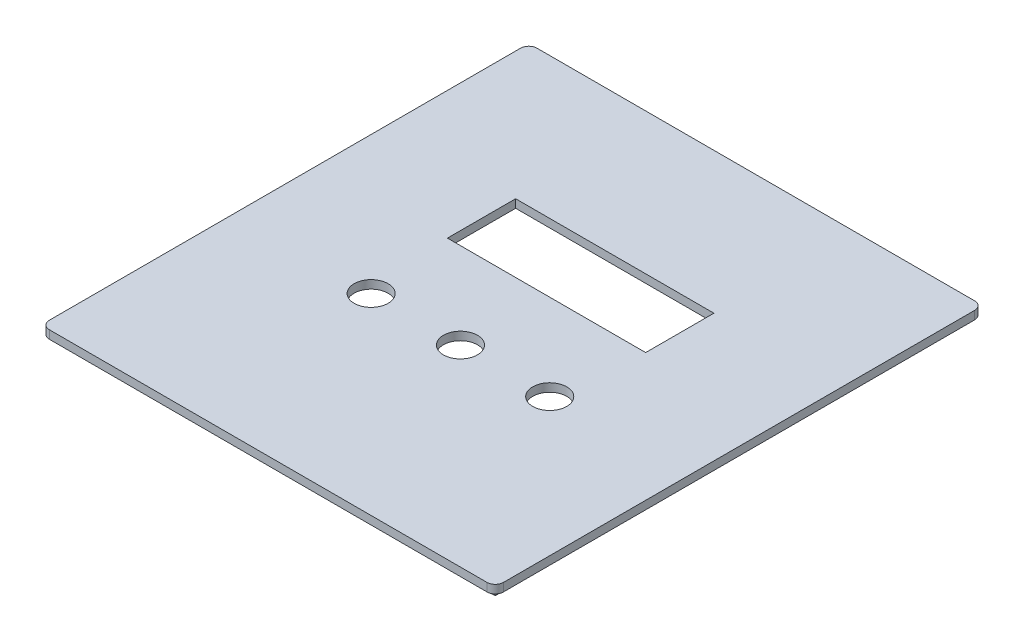
SolidWorks part; units mm, degrees
ref_plane "Front Plane" through (0, 0, 0) normal (0, 0, 1) x (1, 0, 0)
ref_plane "Top Plane" through (0, 0, 0) normal (0, 1, 0) x (1, 0, 0)
ref_plane "Right Plane" through (0, 0, 0) normal (1, 0, 0) x (0, 0, -1)
sketch "Sketch1" plane through (0, 0, 0) normal (0, 1, 0) x (1, 0, 0)
  line L0 (-78.85, 84.92) -> (-78.85, -84.92)
  line L1 (-79.15, 85.22) -> (79.15, 85.22) construction
  line L2 (-79.15, 85.22) -> (-79.15, -85.22) construction
  line L3 (-79.15, -85.22) -> (79.15, -85.22) construction
  line L4 (79.15, 85.22) -> (79.15, -85.22) construction
  line L5 (-79.15, 85.22) -> (79.15, -85.22) construction
  line L6 (-79.15, -85.22) -> (79.15, 85.22) construction
  line L7 (-78.85, -84.92) -> (78.85, -84.92)
  line L8 (78.85, 84.92) -> (78.85, -84.92)
  line L9 (-78.85, 84.92) -> (78.85, 84.92)
  line L10 (-75.85, 81.92) -> (-75.85, -81.92)
  line L11 (-75.85, -81.92) -> (75.85, -81.92)
  line L12 (75.85, 81.92) -> (75.85, -81.92)
  line L13 (-75.85, 81.92) -> (75.85, 81.92)
  point P0 (0, 0)
  dimension "D1" = 158.3
  dimension "D2" = 170.44
  dimension "D3" = 0.3
  dimension "D4" = 3
extrude "Boss-Extrude1" add sketch "Sketch1" along normal blind 3
sketch "Sketch2" plane through (0, 3, 0) normal (0, 1, 0) x (1, 0, 0)
  line L8 (82.15, 88.22) -> (-82.15, 88.22)
  line L9 (-82.15, 88.22) -> (-82.15, -88.22)
  line L10 (-82.15, -88.22) -> (82.15, -88.22)
  line L11 (82.15, -88.22) -> (82.15, 88.22)
  line L12 (82.15, 88.22) -> (-82.15, 88.22)
  line L13 (-82.15, 88.22) -> (-82.15, -88.22)
  line L14 (-82.15, -88.22) -> (82.15, -88.22)
  line L15 (82.15, -88.22) -> (82.15, 88.22)
  dimension "D1" = 3.3
extrude "Boss-Extrude2" add sketch "Sketch2" along normal blind 3
sketch "Sketch3" plane through (0, 6, 0) normal (0, 1, 0) x (1, 0, 0)
  line L0 (0, 88.22) -> (0, -88.22) construction
  line L1 (82.15, 88.22) -> (-82.15, 88.22) construction
  line L2 (-82.15, -88.22) -> (82.15, -88.22) construction
  line L3 (-35.865, 37.18) -> (-35.865, 12.5)
  line L4 (-35.565, 36.88) -> (35.565, 36.88) construction
  line L5 (-35.565, 36.88) -> (-35.565, 12.8) construction
  line L6 (-35.565, 12.8) -> (35.565, 12.8) construction
  line L7 (35.565, 36.88) -> (35.565, 12.8) construction
  line L8 (-35.565, 36.88) -> (35.565, 12.8) construction
  line L9 (-35.565, 12.8) -> (35.565, 36.88) construction
  line L10 (-35.865, 12.5) -> (35.865, 12.5)
  line L11 (35.865, 37.18) -> (35.865, 12.5)
  line L12 (-35.865, 37.18) -> (35.865, 37.18)
  line L13 (-26.155, -18.655) -> (-6.155, -18.655) construction
  line L14 (6.155, -18.655) -> (26.155, -18.655) construction
  line L15 (32.31, -12.5) -> (32.31, 12.5) construction
  line L16 (-82.15, 0) -> (82.15, 0) construction
  line L17 (-82.15, 88.22) -> (-82.15, -88.22) construction
  line L18 (82.15, -88.22) -> (82.15, 88.22) construction
  circle A0 centre (0, -18.655) radius 6.155
  circle A1 centre (32.31, -18.655) radius 6.155
  circle A2 centre (-32.31, -18.655) radius 5.855 construction
  circle A3 centre (-32.31, -18.655) radius 6.155
  point P6 (0, 24.84)
  point P35 (32.31, 0)
  dimension "D4" = 11.71
  dimension "D2" = 71.13
  dimension "D3" = 24.08
  dimension "D6" = 20
  dimension "D7" = 25
  dimension "D1" = 0.3
  dimension "D5" = 0.3
extrude "Cut-Extrude1" cut sketch "Sketch3" against normal up to surface (3 mm away) up to face at (0, 3, 0)
fillet "Fillet1" radius 3 4 edges at (-82.15, 4.5, -88.22) (82.15, 4.5, -88.22) (82.15, 4.5, 88.22) (-82.15, 4.5, 88.22)
